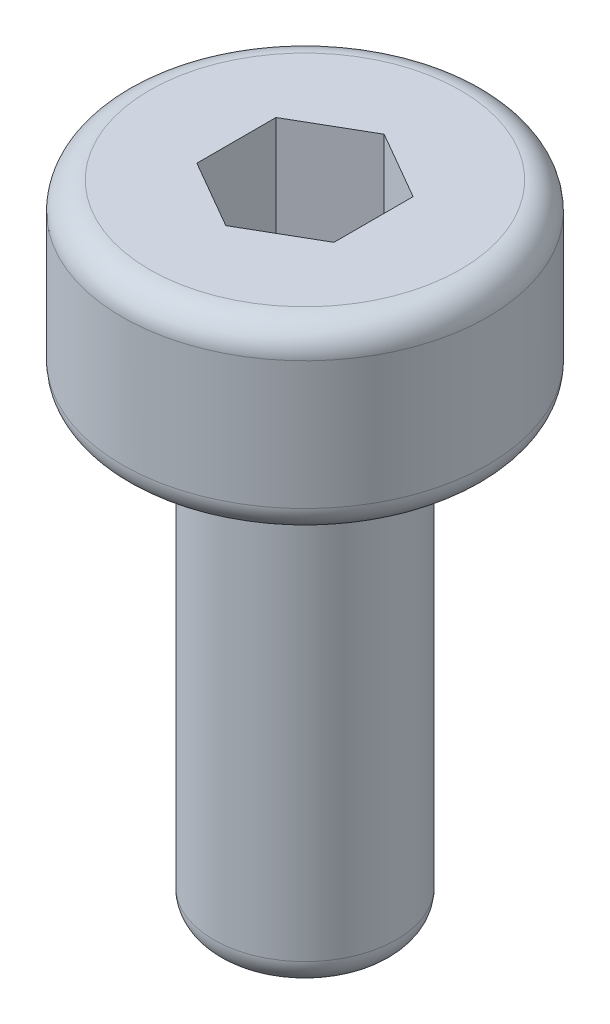
SolidWorks part; units mm, degrees
ref_plane "前视基准面" through (0, 0, 0) normal (0, 0, 1) x (1, 0, 0)
ref_plane "上视基准面" through (0, 0, 0) normal (0, 1, 0) x (1, 0, 0)
ref_plane "右视基准面" through (0, 0, 0) normal (1, 0, 0) x (0, 0, -1)
sketch "草图1" plane through (0, 0, 0) normal (0, 0, 1) x (1, 0, 0)
  line L0 (2, 0) -> (0, 0)
  line L1 (0, 0) -> (0, -2)
  line L2 (0, -2) -> (2, -2)
  line L3 (2, -2) -> (2, 0)
  line L4 (0, 0) -> (0, -2) construction
  dimension "D1" = 2
  dimension "D2" = 2
revolve "旋转1" add sketch "草图1" angle 360 about L4
sketch "草图2" plane through (0, -2, 0) normal (0, -1, 0) x (1, 0, 0)
  circle A0 centre (0, 0) radius 1
  dimension "D1" = 2
extrude "凸台-拉伸1" add sketch "草图2" along normal blind 5
sketch "草图3" plane through (0, 0, 0) normal (0, 1, 0) x (-1, 0, 0)
  line L7 (0, -0.866) -> (0.75, -0.433)
  line L8 (0.75, -0.433) -> (0.75, 0.433)
  line L9 (0.75, 0.433) -> (0, 0.866)
  line L10 (0, 0.866) -> (-0.75, 0.433)
  line L11 (-0.75, 0.433) -> (-0.75, -0.433)
  line L12 (-0.75, -0.433) -> (0, -0.866)
  circle A0 centre (0, 0) radius 0.75 construction
  dimension "D1" = 1.5
extrude "切除-拉伸1" cut sketch "草图3" against normal blind 1.5
fillet "圆角1" radius 0.3 3 edges at (0, -7, -1) (2, 0, 0) (2, -2, 0)
